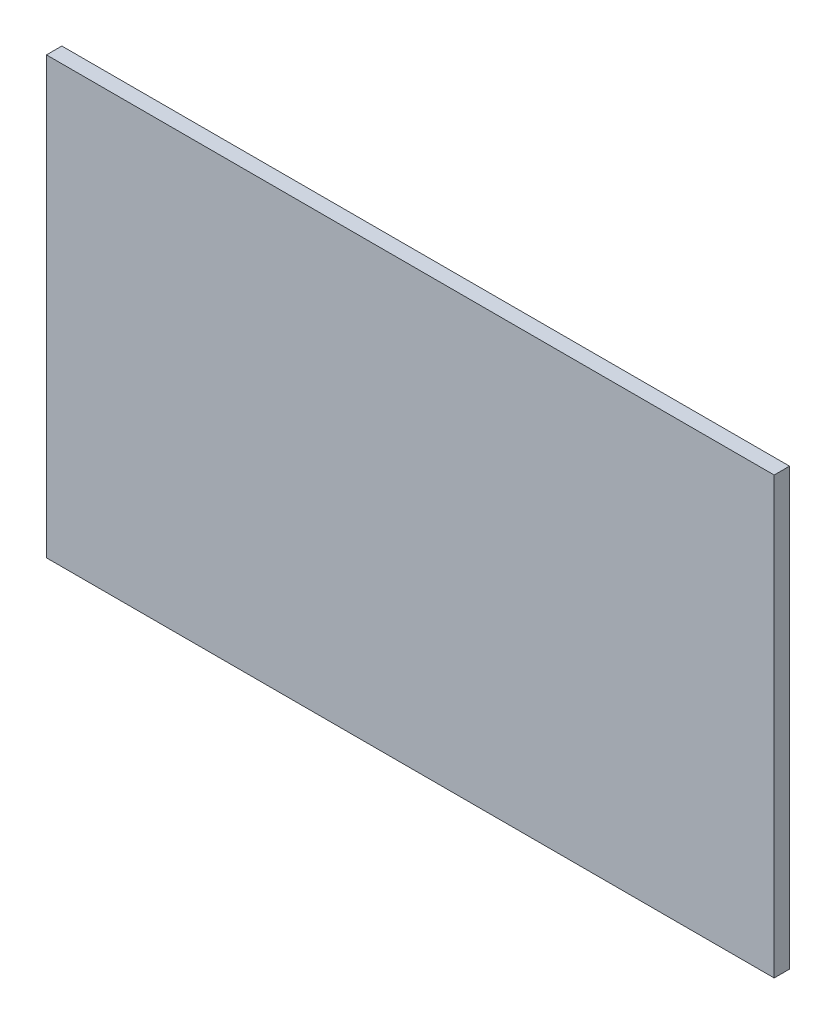
SolidWorks part; units mm, degrees
material "Vidro"
ref_plane "Plano frontal" through (0, 0, 0) normal (0, 0, 1) x (1, 0, 0)
ref_plane "Plano superior" through (0, 0, 0) normal (0, 1, 0) x (1, 0, 0)
ref_plane "Plano direito" through (0, 0, 0) normal (1, 0, 0) x (0, 0, -1)
sketch "Esboço1" plane through (0, 0, 0) normal (0, 0, 1) x (1, 0, 0)
  line L1 (-75.175, -45) -> (75.175, -45)
  line L2 (-75.175, -45) -> (-75.175, 45)
  line L3 (-75.175, 45) -> (75.175, 45)
  line L4 (75.175, -45) -> (75.175, 45)
  point P4 (0, 45)
  point P6 (75.175, 0)
  dimension "D1" = 90
  dimension "D2" = 150.35
extrude "Ressalto-extrusão1" add sketch "Esboço1" along normal blind 3.175
